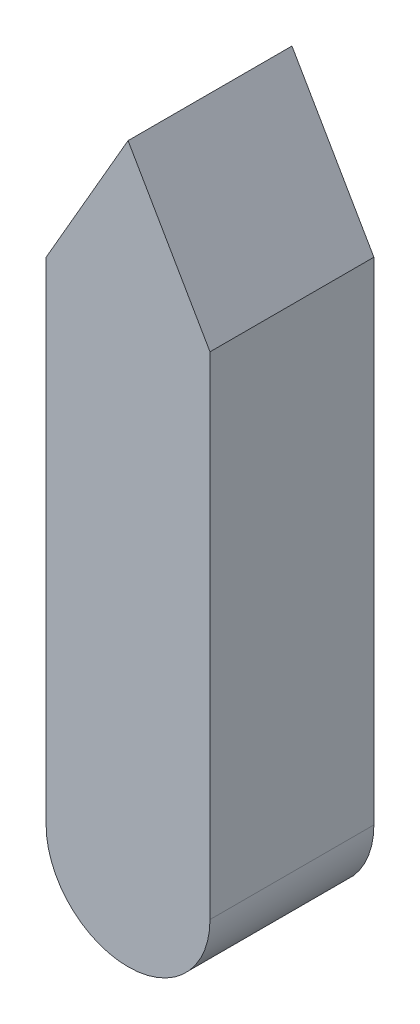
SolidWorks part; units mm, degrees
ref_plane "Front Plane" through (0, 0, 0) normal (0, 0, 1) x (1, 0, 0)
ref_plane "Top Plane" through (0, 0, 0) normal (0, 1, 0) x (1, 0, 0)
ref_plane "Right Plane" through (0, 0, 0) normal (1, 0, 0) x (0, 0, -1)
curve "Curva1"
  spline degree 3 poles (197.9645, -34.9357, 0) (201.0162, 0.0157, 0) (197.9584, 35.0151, 0) (190.9535, 69.875, 0) (181.2428, 105.4135, 0) (168.4309, 142.35, 0) (150.666, 180.4926, 0) (125.6418, 218.1495, 0) (91.7977, 252.1104, 0) (49.247, 278.3402, 0) (0.1173, 293.2033, 0) (-51.9656, 294.7473, 0) (-103.1744, 283.3184, 0) (-150.7833, 261.1198, 0) (-193.8148, 230.9842, 0) (-230.9839, 193.8175, 0) (-261.1298, 150.7635, 0) (-283.3428, 103.1285, 0) (-296.9458, 52.3587, 0) (-301.5276, 0.0065, 0) (-296.9458, -52.3383, 0) (-282.7225, -102.8678, 0) (-258.8954, -149.4236, 0) (-226.2386, -189.7709, 0) (-186.287, -221.9155, 0) (-141.1976, -244.4002, 0) (-93.5105, -256.562, 0) (-45.7838, -258.6102, 0) (-0.254, -251.5019, 0) (41.4169, -236.7553, 0) (78.2655, -216.1133, 0) (109.962, -191.2099, 0) (136.6518, -163.3704, 0) (158.6787, -133.4692, 0) (176.2979, -101.9593, 0) (189.5095, -69.0499, 0) (197.9645, -34.9357, 0) (201.0162, 0.0157, 0) (197.9584, 35.0151, 0) knots -0.063898 -0.042464 -0.021206 0 0.021221 0.042648 0.064804 0.08839 0.113898 0.141369 0.170458 0.200678 0.231618 0.26301 0.294674 0.326455 0.358255 0.390056 0.421856 0.453656 0.485457 0.517257 0.549051 0.580803 0.612427 0.643806 0.674801 0.705259 0.735021 0.763922 0.791813 0.818573 0.844139 0.868527 0.891845 0.914288 0.936102 0.957536 0.978794 1 1.021221 1.042648 1.064804 periodic
sketch "Croquis1" plane through (0, 0, 0) normal (0, 0, 1) x (1, 0, 0)
  circle A0 centre (0, 0) radius 90
  spline S0 degree 3 poles (197.9645, -34.9357) (201.0162, 0.0157) (197.9584, 35.0151) (190.9535, 69.875) (181.2428, 105.4135) (168.4309, 142.35) (150.666, 180.4926) (125.6418, 218.1495) (91.7977, 252.1104) (49.247, 278.3402) (0.1173, 293.2033) (-51.9656, 294.7473) (-103.1744, 283.3184) (-150.7833, 261.1198) (-193.8148, 230.9842) (-230.9839, 193.8175) (-261.1298, 150.7635) (-283.3428, 103.1285) (-296.9458, 52.3587) (-301.5276, 0.0065) (-296.9458, -52.3383) (-282.7225, -102.8678) (-258.8954, -149.4236) (-226.2386, -189.7709) (-186.287, -221.9155) (-141.1976, -244.4002) (-93.5105, -256.562) (-45.7838, -258.6102) (-0.254, -251.5019) (41.4169, -236.7553) (78.2655, -216.1133) (109.962, -191.2099) (136.6518, -163.3704) (158.6787, -133.4692) (176.2979, -101.9593) (189.5095, -69.0499) (197.9645, -34.9357) (201.0162, 0.0157) (197.9584, 35.0151) knots -0.063898 -0.042464 -0.021206 0 0.021221 0.042648 0.064804 0.08839 0.113898 0.141369 0.170458 0.200678 0.231618 0.26301 0.294674 0.326455 0.358255 0.390056 0.421856 0.453656 0.485457 0.517257 0.549051 0.580803 0.612427 0.643806 0.674801 0.705259 0.735021 0.763922 0.791813 0.818573 0.844139 0.868527 0.891845 0.914288 0.936102 0.957536 0.978794 1 1.021221 1.042648 1.064804 only from (200, 0) to (200, 0) construction
  spline S1 degree 3 poles (197.9645, -34.9357) (201.0162, 0.0157) (197.9584, 35.0151) (190.9535, 69.875) (181.2428, 105.4135) (168.4309, 142.35) (150.666, 180.4926) (125.6418, 218.1495) (91.7977, 252.1104) (49.247, 278.3402) (0.1173, 293.2033) (-51.9656, 294.7473) (-103.1744, 283.3184) (-150.7833, 261.1198) (-193.8148, 230.9842) (-230.9839, 193.8175) (-261.1298, 150.7635) (-283.3428, 103.1285) (-296.9458, 52.3587) (-301.5276, 0.0065) (-296.9458, -52.3383) (-282.7225, -102.8678) (-258.8954, -149.4236) (-226.2386, -189.7709) (-186.287, -221.9155) (-141.1976, -244.4002) (-93.5105, -256.562) (-45.7838, -258.6102) (-0.254, -251.5019) (41.4169, -236.7553) (78.2655, -216.1133) (109.962, -191.2099) (136.6518, -163.3704) (158.6787, -133.4692) (176.2979, -101.9593) (189.5095, -69.0499) (197.9645, -34.9357) (201.0162, 0.0157) (197.9584, 35.0151) knots -0.063898 -0.042464 -0.021206 0 0.021221 0.042648 0.064804 0.08839 0.113898 0.141369 0.170458 0.200678 0.231618 0.26301 0.294674 0.326455 0.358255 0.390056 0.421856 0.453656 0.485457 0.517257 0.549051 0.580803 0.612427 0.643806 0.674801 0.705259 0.735021 0.763922 0.791813 0.818573 0.844139 0.868527 0.891845 0.914288 0.936102 0.957536 0.978794 1 1.021221 1.042648 1.064804 only from (200, 0) to (200, 0)
  dimension "D1" = 180
extrude "Saliente-Extruir1" [suppressed] add sketch "Croquis1" along normal mid plane 100
sketch "Croquis2" plane through (0, 0, 0) normal (0, 0, 1) x (1, 0, 0)
  line L0 (-50, 150) -> (0, 236.6025)
  line L1 (50, -150) -> (-50, -150)
  line L2 (50, -150) -> (50, 150)
  line L3 (50, 150) -> (-50, 150)
  line L4 (-50, -150) -> (-50, 150)
  line L5 (50, -150) -> (-50, 150) construction
  line L6 (50, 150) -> (-50, -150) construction
  line L7 (0, 236.6025) -> (50, 150)
  arc A0 (-50, -150) -> (50, -150) centre (0, -150) ccw
  point P0 (0, 0)
  dimension "D1" = 50
  dimension "D2" = 300
extrude "Saliente-Extruir2" add sketch "Croquis2" along normal mid plane 100 contours L7 L0 L3 | L4 L1 L2 L3 | L1 A0
